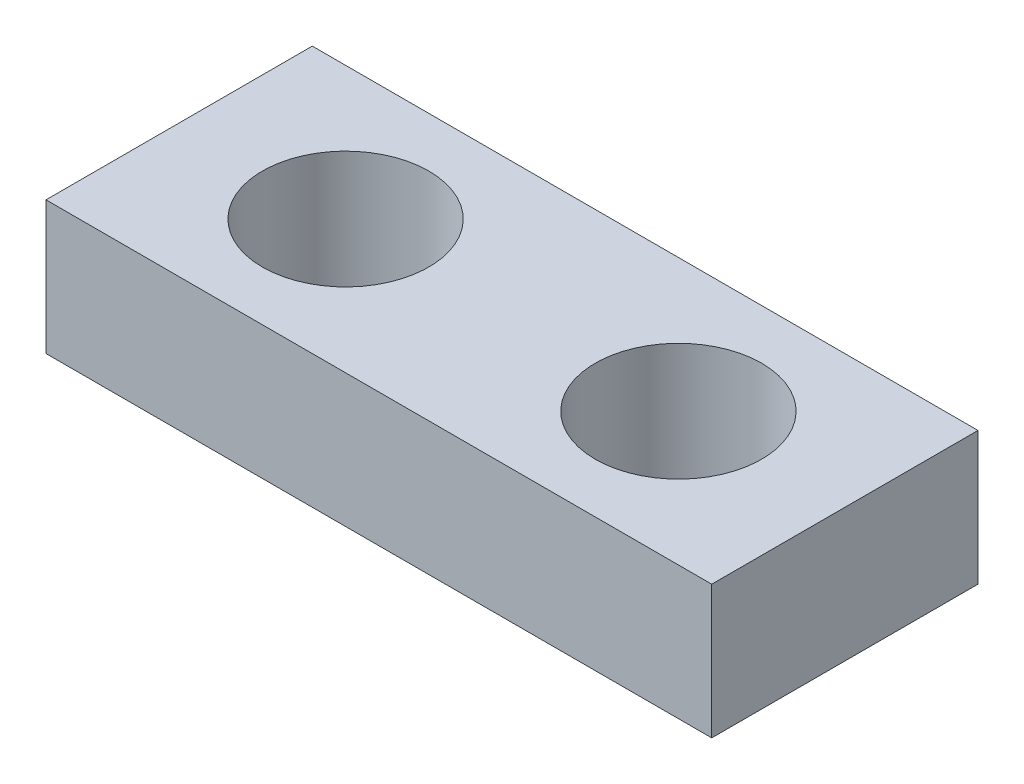
SolidWorks part; units mm, degrees
ref_plane "Front Plane" through (0, 0, 0) normal (0, 0, 1) x (1, 0, 0)
ref_plane "Top Plane" through (0, 0, 0) normal (0, 1, 0) x (1, 0, 0)
ref_plane "Right Plane" through (0, 0, 0) normal (1, 0, 0) x (0, 0, -1)
sketch "Sketch1" plane through (0, 0, 0) normal (0, 1, 0) x (1, 0, 0)
  line L1 (0, 0) -> (127, 0)
  line L2 (0, 0) -> (0, 50.8)
  line L3 (0, 50.8) -> (127, 50.8)
  line L4 (127, 0) -> (127, 50.8)
  dimension "D1" = 127
  dimension "D2" = 50.8
extrude "Boss-Extrude1" add sketch "Sketch1" along normal blind 25.4
sketch "Sketch2" plane through (0, 25.4, 0) normal (0, 1, 0) x (1, 0, 0)
  line L0 (0, 50.8) -> (0, 0) construction
  line L1 (0, 25.4) -> (31.75, 25.4) construction
  line L2 (95.25, 25.4) -> (127, 25.4) construction
  line L3 (127, 0) -> (127, 50.8) construction
  circle A0 centre (31.75, 25.4) radius 15.875
  circle A1 centre (95.25, 25.4) radius 15.875
  point P6 (0, 25.4)
  dimension "D1" = 31.75
  dimension "D2" = 31.75
extrude "Cut-Extrude1" cut sketch "Sketch2" against normal through all
